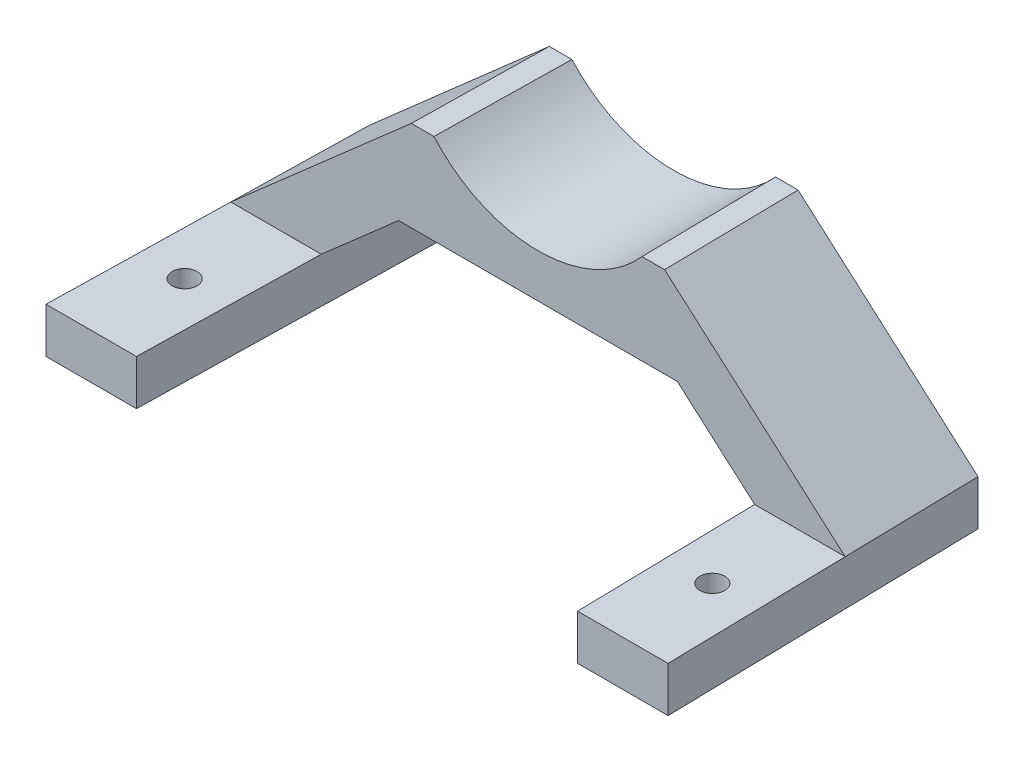
SolidWorks part; units mm, degrees
ref_plane "Front Plane" through (0, 0, 0) normal (0, 0, 1) x (1, 0, 0)
ref_plane "Top Plane" through (0, 0, 0) normal (0, 1, 0) x (1, 0, 0)
ref_plane "Right Plane" through (0, 0, 0) normal (1, 0, 0) x (0, 0, -1)
sketch "Sketch1" plane through (0, 0, 0) normal (0, 1, 0) x (1, 0, 0)
  line L0 (0, 0) -> (20.0045, 0)
  line L1 (20.0045, 0) -> (21.4891, 70)
  line L2 (21.4891, 70) -> (1.4846, 70)
  line L3 (1.4846, 70) -> (0, 0)
  line L4 (68.7637, 0) -> (68.7637, 140) construction
  line L5 (21.4891, 70) -> (22.9737, 140) construction
  line L6 (116.0384, 70) -> (136.0429, 70)
  line L7 (117.523, 0) -> (116.0384, 70)
  line L8 (137.5275, 0) -> (117.523, 0)
  line L9 (136.0429, 70) -> (137.5275, 0)
  line L10 (0.4332, 20.4241) -> (20.4287, 20) construction
  circle A0 centre (10.4309, 20.212) radius 2.75
  circle A2 centre (127.0966, 20.212) radius 2.75
  dimension "D6" = 5.5
  dimension "D1" = 1.215
  dimension "D2" = 45.79
  dimension "D3" = 20
  dimension "D4" = 70
  dimension "D5" = 140
  dimension "D7" = 20
extrude "Boss-Extrude1" add sketch "Sketch1" along normal blind 10
sketch "Sketch2" plane through (0, 0, -70) normal (0, 0, -1) x (-1, 0, 0)
  line L0 (-21.4891, 10) -> (-1.4846, 10) construction
  line L1 (-116.0384, 10) -> (-21.4891, 10) construction
  line L2 (-68.7637, 10) -> (-68.7637, 35) construction
  line L3 (-91.2637, 45) -> (-96.2637, 45)
  line L4 (-46.2637, 45) -> (-41.2637, 45)
  line L5 (-98.9902, 25) -> (-38.5373, 25)
  line L6 (-38.5373, 25) -> (-21.4891, 10)
  line L7 (-98.9902, 25) -> (-116.0384, 10)
  line L8 (-116.0384, 10) -> (-136.0429, 10)
  line L9 (-136.0429, 10) -> (-96.2637, 45)
  line L10 (-41.2637, 45) -> (-1.4846, 10)
  line L11 (-1.4846, 10) -> (-21.4891, 10)
  arc A0 (-91.2637, 45) -> (-46.2637, 45) centre (-68.7637, 65.3125) ccw
  point P3 (-68.7637, 35)
  dimension "D5" = 45
  dimension "D1" = 25
  dimension "D2" = 5
  dimension "D3" = 10
  dimension "D4" = 10
ref_plane "Plane1" through (0, 0, -40) normal (0, 0, -1) x (-1, 0, 0)
sketch "Sketch3" plane through (0, 0, -40) normal (0, 0, -1) x (-1, 0, 0)
  line L0 (-136.6791, 10) -> (-96.7637, 45)
  line L1 (-96.7637, 45) -> (-91.7637, 45)
  line L2 (-99.568, 25) -> (-37.9595, 25)
  line L3 (-68.7637, 10) -> (-68.7637, 35) construction
  line L4 (-68.7637, 10) -> (-68.7637, 35) construction
  line L5 (-45.7637, 45) -> (-40.7637, 45)
  line L6 (-40.7637, 45) -> (-0.8484, 10)
  line L7 (-0.8484, 10) -> (-20.8529, 10)
  line L8 (-20.8529, 10) -> (-37.9595, 25)
  line L9 (-99.568, 25) -> (-116.6746, 10)
  line L10 (-116.6746, 10) -> (-136.6791, 10)
  line L11 (-98.9902, 25) -> (-38.5373, 25) construction
  line L19 (-91.2637, 45) -> (-96.2637, 45) construction
  arc A0 (-91.7637, 45) -> (-45.7637, 45) centre (-68.7637, 65.3125) ccw
  point P26 (-68.7637, 34.627)
  dimension "D1" = 5
  dimension "D2" = 46
loft "Loft1" add profiles "Sketch2", "Sketch3"
